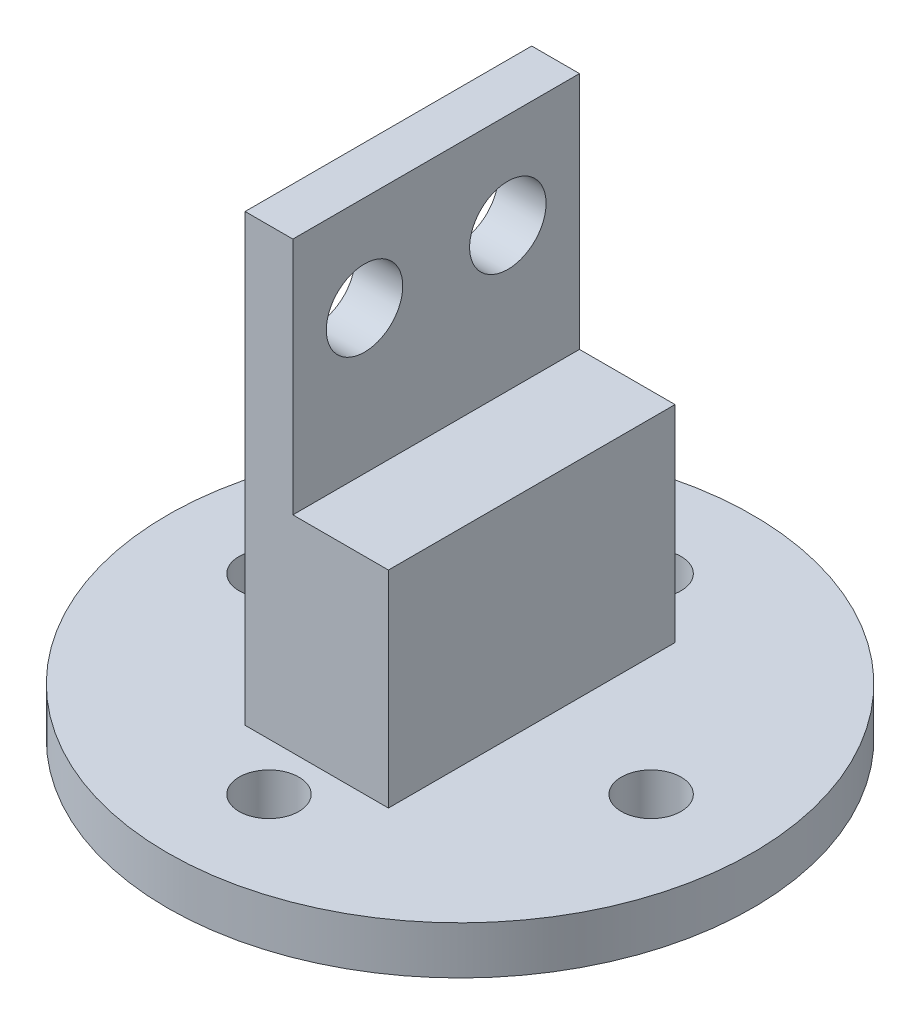
SolidWorks part; units mm, degrees
ref_plane "Front" through (0, 0, 0) normal (0, 0, 1) x (1, 0, 0)
ref_plane "Top" through (0, 0, 0) normal (0, 1, 0) x (1, 0, 0)
ref_plane "Right" through (0, 0, 0) normal (1, 0, 0) x (0, 0, -1)
sketch "草图1" plane through (0, 0, 0) normal (0, 1, 0) x (1, 0, 0)
  line L0 (0, 0) -> (8, 0) construction
  circle A0 centre (0, 0) radius 12.25
  circle A2 centre (8, 0) radius 1.25
  circle A3 centre (0, -8) radius 1.25
  circle A4 centre (-8, 0) radius 1.25
  circle A5 centre (0, 8) radius 1.25
  point P15 (0, 0)
  dimension "D1" = 4
extrude "凸台-拉伸1" add sketch "草图1" along normal blind 2
sketch "草图2" plane through (0, 2, 0) normal (0, 1, 0) x (1, 0, 0)
  circle A0 centre (0, 0) radius 3
extrude "凸台-拉伸2" add sketch "草图2" along normal blind 10.63
sketch "草图3" plane through (0, 12.63, 0) normal (0, 1, 0) x (1, 0, 0)
  line L0 (0, 0) -> (-1, 0) construction
  line L1 (-1, 0) -> (-1, 6) construction
  line L2 (-1, 6) -> (-3, 6) construction
  line L3 (-3, 6) -> (-3, 0) construction
  line L4 (-3, 0) -> (-3, -6) construction
  line L5 (-3, -6) -> (-1, -6) construction
  line L6 (-1, -6) -> (-1, 0) construction
  line L7 (-3, 6) -> (-1, 6)
  line L9 (-1, -6) -> (-3, -6)
  line L10 (-3, -6) -> (-3, 6)
  line L11 (-1, 6) -> (-1, -6)
  circle A0 centre (0, 0) radius 3 construction
  circle A1 centre (0, 0) radius 3 construction
extrude "凸台-拉伸3" add sketch "草图3" along normal blind 8
sketch "草图5" plane through (-1, 0, 0) normal (1, 0, 0) x (0, 0, -1)
  line L0 (0, 12.63) -> (0, 16.63) construction
  line L1 (-2.8284, 12.63) -> (2.8284, 12.63) construction
  line L2 (0, 16.63) -> (3, 16.63) construction
  circle A0 centre (3, 16.63) radius 1.6
  circle A1 centre (-3, 16.63) radius 1.6
extrude "切除-拉伸1" cut sketch "草图5" against normal blind 10
sketch "草图6" plane through (0, 2, 0) normal (0, 1, 0) x (1, 0, 0)
  line L0 (-3, 0) -> (-3, 6) construction
  line L1 (-3, 6) -> (-3, -6) construction
  line L2 (-1, 6) -> (-3, 6) construction
  line L3 (-3, 6) -> (3, 6) construction
  line L4 (3, 6) -> (3, 0) construction
  line L5 (-3, -6) -> (-3, 6)
  line L6 (-3, 6) -> (3, 6)
  line L7 (3, 6) -> (3, -6)
  line L8 (-3, 0) -> (0, 0) construction
  line L9 (-3, -6) -> (3, -6)
  arc A0 (-1, -2.8284) -> (-1, 2.8284) centre (0, 0) ccw construction
extrude "凸台-拉伸4" add sketch "草图6" along normal blind 10.63
sketch "草图7" plane through (0, 12.63, 0) normal (0, 1, 0) x (1, 0, 0)
  line L0 (-1, 6) -> (3, 6)
  line L1 (3, 6) -> (3, -6)
  line L2 (3, -6) -> (-1, -6)
  line L3 (-1, -6) -> (-1, 6)
extrude "切除-拉伸2" cut sketch "草图7" against normal blind 2
